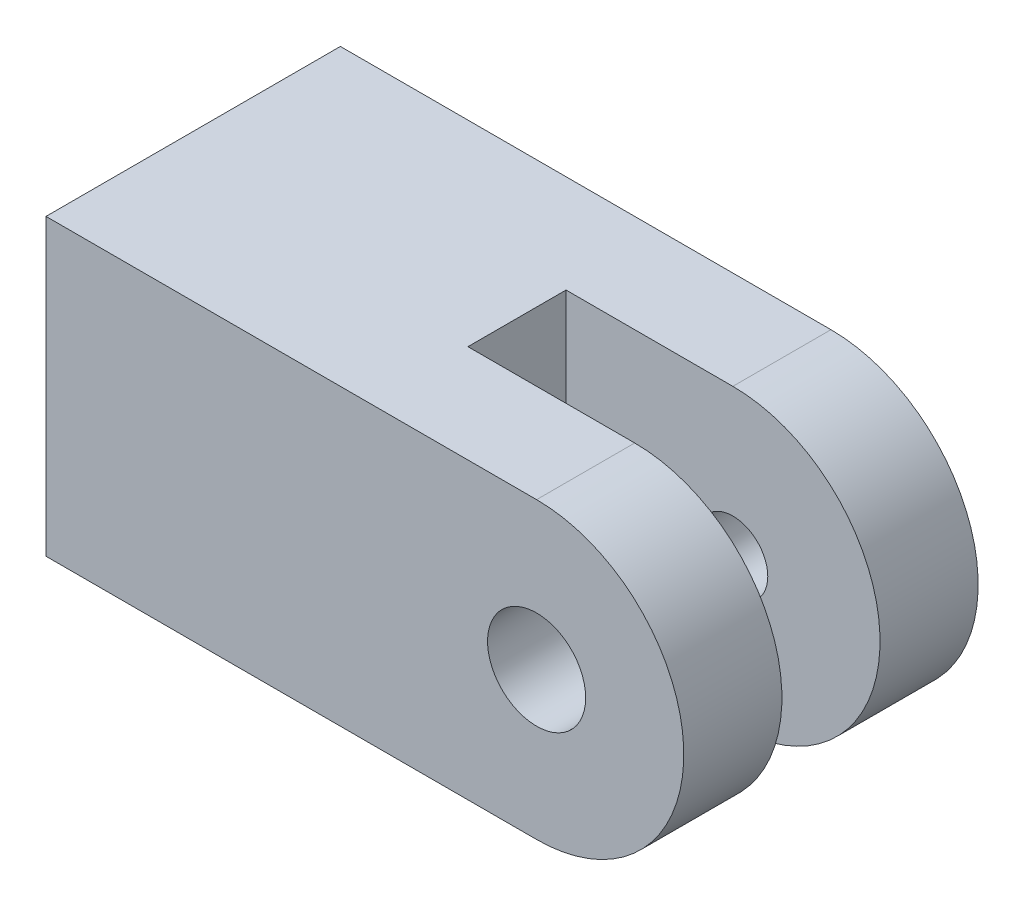
SolidWorks part; units mm, degrees
material "6061-T6 (SS)"
ref_plane "Front Plane" through (0, 0, 0) normal (0, 0, 1) x (1, 0, 0)
ref_plane "Top Plane" through (0, 0, 0) normal (0, 1, 0) x (1, 0, 0)
ref_plane "Right Plane" through (0, 0, 0) normal (1, 0, 0) x (0, 0, -1)
sketch "Sketch2" plane through (0, 0, 0) normal (0, 0, 1) x (1, 0, 0)
  line L0 (0, 4.7625) -> (0, -4.7625) construction
  line L5 (-9.525, 4.7625) -> (0, 4.7625)
  line L6 (-9.525, 4.7625) -> (-9.525, -4.7625)
  line L7 (-9.525, -4.7625) -> (0, -4.7625)
  line L9 (-9.525, 4.7625) -> (0, 0) construction
  line L10 (-9.525, -4.7625) -> (0, 0) construction
  arc A0 (0, 4.7625) -> (0, -4.7625) centre (0, 0) cw
  point P0 (0, 0)
  dimension "D3" = 4.7625
  dimension "D1" = 9.525
  dimension "D2" = 9.525
extrude "Boss-Extrude2" add sketch "Sketch2" along normal mid plane 9.525
ref_plane "Plane1" through (4.7625, 0, 0) normal (1, 0, 0) x (0, 0, -1)
sketch "Sketch3" plane through (4.7625, 0, 0) normal (1, 0, 0) x (0, 0, -1)
  line L0 (-4.7625, -4.7625) -> (4.7625, -4.7625) construction
  line L1 (-1.5875, 4.7625) -> (1.5875, 4.7625)
  line L2 (-1.5875, 4.7625) -> (-1.5875, -4.7625)
  line L3 (-1.5875, -4.7625) -> (1.5875, -4.7625)
  line L4 (1.5875, 4.7625) -> (1.5875, -4.7625)
  line L5 (-1.5875, 4.7625) -> (1.5875, -4.7625) construction
  line L6 (-1.5875, -4.7625) -> (1.5875, 4.7625) construction
  point P0 (0, 0)
  dimension "D1" = 3.175
extrude "Cut-Extrude1" cut sketch "Sketch3" against normal blind 10.16
sketch "Sketch4" plane through (-9.525, 0, 0) normal (-1, 0, 0) x (0, 0, 1)
  line L4 (-4.7625, 4.7625) -> (-4.7625, -4.7625)
  line L5 (-4.7625, -4.7625) -> (4.7625, -4.7625)
  line L6 (4.7625, -4.7625) -> (4.7625, 4.7625)
  line L7 (4.7625, 4.7625) -> (-4.7625, 4.7625)
  line L8 (-4.7625, 4.7625) -> (-4.7625, -4.7625)
  line L9 (-4.7625, -4.7625) -> (4.7625, -4.7625)
  line L10 (4.7625, -4.7625) -> (4.7625, 4.7625)
  line L11 (4.7625, 4.7625) -> (-4.7625, 4.7625)
  dimension "D1" = 0
extrude "Boss-Extrude3" add sketch "Sketch4" along normal blind 6.35
hole_wizard "#8-32 Tapped Hole1" positions "Sketch5" profile "Sketch6" tap size "#8-32" standard "ANSI Inch"
sketch "Sketch5" plane through (-15.875, 0, 0) normal (-1, 0, 0) x (0, 0, 1)
  point P0 (0, 0)
sketch "Sketch6" plane through (-15.875, 0, 0) normal (0, 1, 0) x (0, 0, 1)
  line L0 (0, 0) -> (0, 10.5628)
  line L1 (0, 10.5628) -> (1.7272, 9.525)
  line L2 (1.7272, 9.525) -> (1.7272, 0)
  line L5 (1.7272, 0) -> (0, 0)
  line L10 (0, 10.5628) -> (-1.7272, 9.525) construction
  line L11 (0, -6.35) -> (0, 107.95) construction
  dimension "Tap Drill Dia." = 3.4544
  dimension "Tap Drill Depth" = 9.525
  dimension "Drill Angle" = 118
cosmetic thread "Hole Thread1" parameters "D1"=8.3312, "D2"=4.1656
hole_wizard "1/8 (0.125) Diameter Hole1" positions "Sketch9" profile "Sketch8" hole size "1/8" standard "ANSI Inch" end condition up to next
sketch "Sketch9" plane through (0, 0, 4.7625) normal (0, 0, 1) x (1, 0, 0)
  point P0 (0, 0)
sketch "Sketch8" plane through (0, 0, 4.7625) normal (1, 0, 0) x (0, -1, 0)
  line L0 (0, 0) -> (0, 3.175)
  line L1 (0, 3.175) -> (1.5875, 3.175)
  line L2 (1.5875, 3.175) -> (1.5875, 0)
  line L5 (1.5875, 0) -> (0, 0)
  line L11 (0, -6.35) -> (0, 107.95) construction
  dimension "Thru Hole Dia." = 3.175
  dimension "Thru Hole Depth" = 3.175
hole_wizard "#4-40 Tapped Hole1" positions "Sketch10" profile "Sketch11" tap size "#4-40" standard "ANSI Inch" end condition through all
sketch "Sketch10" plane through (0, 0, -1.5875) normal (0, 0, 1) x (1, 0, 0)
  point P0 (0, 0)
sketch "Sketch11" plane through (0, 0, -1.5875) normal (1, 0, 0) x (0, -1, 0)
  line L0 (0, 0) -> (0, 3.175)
  line L1 (0, 3.175) -> (1.1303, 3.175)
  line L2 (1.1303, 3.175) -> (1.1303, 0)
  line L5 (1.1303, 0) -> (0, 0)
  line L11 (0, -6.35) -> (0, 107.95) construction
  dimension "Thru Tap Drill Dia." = 2.2606
  dimension "Thru Tap Drill Depth" = 3.175
cosmetic thread "Hole Thread2" parameters "D2"=2.8448
